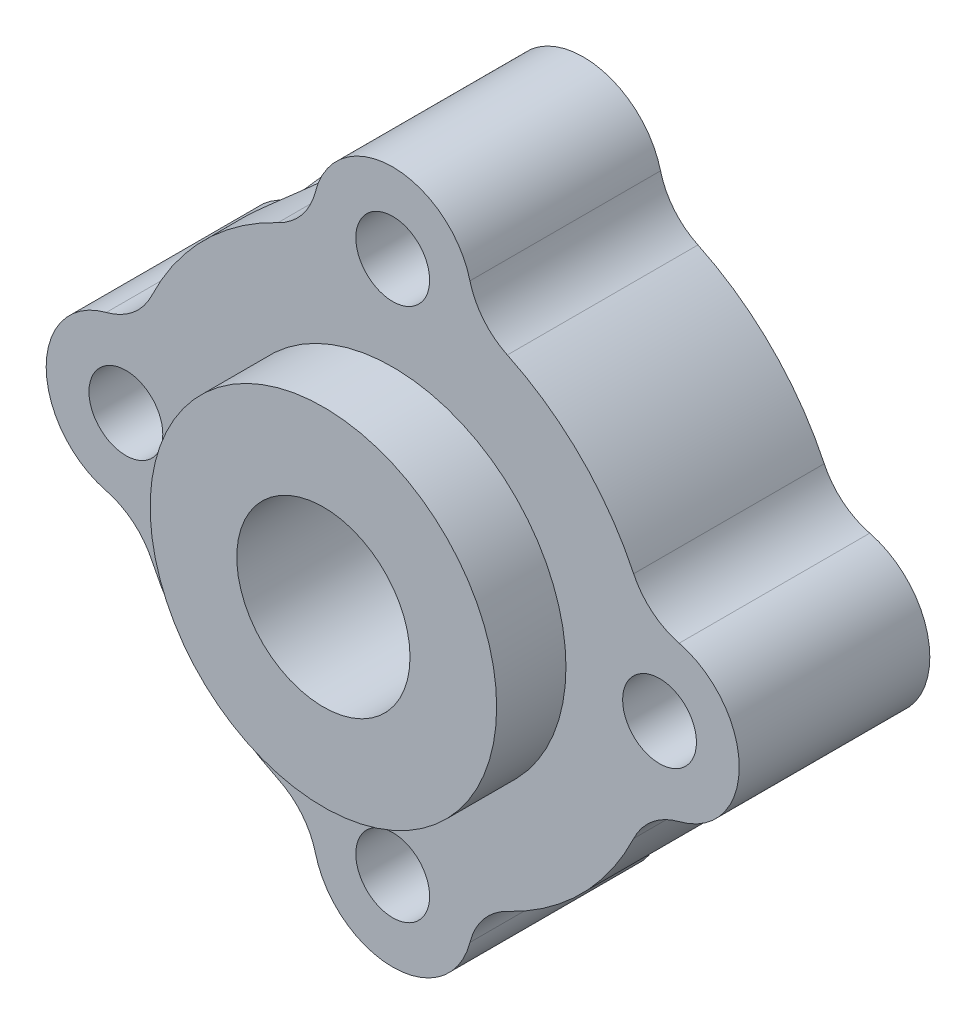
SolidWorks part; units mm, degrees
ref_plane "Front Plane" through (0, 0, 0) normal (0, 0, 1) x (1, 0, 0)
ref_plane "Top Plane" through (0, 0, 0) normal (0, 1, 0) x (1, 0, 0)
ref_plane "Right Plane" through (0, 0, 0) normal (1, 0, 0) x (0, 0, -1)
sketch "Sketch1" plane through (0, 0, 0) normal (0, 0, 1) x (1, 0, 0)
  arc A0 (-21.7959, 25.8991) -> (-28.2504, 19.4446) centre (-18.9077, 16.5564) ccw
  arc A1 (-28.2504, 13.6681) -> (-21.7959, 7.2136) centre (-18.9077, 16.5564) ccw
  arc A2 (-16.0195, 25.8991) -> (-21.7959, 25.8991) centre (-18.9077, 26.3354) ccw
  arc A3 (-21.7959, 7.2136) -> (-16.0195, 7.2136) centre (-18.9077, 6.7774) ccw
  arc A4 (-28.2504, 19.4446) -> (-28.2504, 13.6681) centre (-28.6867, 16.5564) ccw
  arc A5 (-9.565, 13.6681) -> (-9.565, 19.4446) centre (-9.1287, 16.5564) ccw
  arc A6 (-9.565, 19.4446) -> (-16.0195, 25.8991) centre (-18.9077, 16.5564) ccw
  arc A7 (-16.0195, 7.2136) -> (-9.565, 13.6681) centre (-18.9077, 16.5564) ccw
  dimension "D1" = 19.558
extrude "Boss-Extrude2" add sketch "Sketch1" along normal blind 6.985
fillet "Fillet3" radius 2.54 8 edges at (-9.565, 13.6681, 3.4925) (-16.0195, 7.2136, 3.4925) (-21.7959, 7.2136, 3.4925) (-28.2504, 13.6681, 3.4925) (-9.565, 19.4446, 3.4925) (-16.0195, 25.8991, 3.4925) (-21.7959, 25.8991, 3.4925) (-28.2504, 19.4446, 3.4925)
sketch "Sketch2" plane through (0, 0, 6.985) normal (0, 0, 1) x (1, 0, 0)
  line L0 (-31.6077, 16.5564) -> (-6.2077, 16.5564) construction
  arc A0 (-29.4061, 19.3874) -> (-29.4061, 13.7254) centre (-28.6867, 16.5564) ccw construction
  arc A1 (-8.4093, 13.7254) -> (-8.4093, 19.3874) centre (-9.1287, 16.5564) ccw construction
  circle A2 centre (-18.9077, 16.5564) radius 6.35
extrude "Boss-Extrude3" add sketch "Sketch2" along normal blind 2.54
sketch "Sketch3" plane through (0, 0, 9.525) normal (0, 0, 1) x (1, 0, 0)
  line L0 (-25.2577, 16.5564) -> (-12.5577, 16.5564) construction
  circle A0 centre (-18.9077, 16.5564) radius 6.35 construction
  circle A1 centre (-18.9077, 16.5564) radius 3.175
  dimension "D1" = 6.35
extrude "Cut-Extrude1" cut sketch "Sketch3" against normal blind 9.525
sketch "Sketch4" plane through (0, 0, 0) normal (0, 0, -1) x (-1, 0, 0)
  circle A2 centre (18.9077, 16.5564) radius 9.779
  dimension "D1" = 19.558
sketch "Sketch5" plane through (0, 0, 0) normal (0, 0, -1) x (-1, 0, 0)
  line L0 (18.9077, 29.2564) -> (18.9077, 3.8564) construction
  line L1 (6.2077, 16.5564) -> (31.6077, 16.5564) construction
  arc A0 (21.7387, 27.0548) -> (16.0767, 27.0548) centre (18.9077, 26.3354) ccw construction
  arc A1 (16.0767, 6.0579) -> (21.7387, 6.0579) centre (18.9077, 6.7774) ccw construction
  arc A2 (8.4093, 19.3874) -> (8.4093, 13.7254) centre (9.1287, 16.5564) ccw construction
  arc A3 (29.4061, 13.7254) -> (29.4061, 19.3874) centre (28.6867, 16.5564) ccw construction
hole_wizard "#6-32 Tapped Hole1" positions "Sketch7" profile "Sketch6" tap size "#6-32" standard "ANSI Inch" end condition through all
sketch "Sketch7" plane through (0, 0, 0) normal (0, 0, -1) x (-1, 0, 0)
  line L0 (18.9077, 29.2564) -> (18.9077, 3.8564) construction
  line L1 (6.2077, 16.5564) -> (31.6077, 16.5564) construction
  circle A0 centre (18.9077, 16.5564) radius 9.779 construction
  point P0 (18.9077, 26.3354)
  point P6 (28.6867, 16.5564)
  point P9 (18.9077, 6.7774)
  point P12 (9.1287, 16.5564)
sketch "Sketch6" plane through (-18.9077, 26.3354, 0) normal (1, 0, 0) x (0, 1, 0)
  line L0 (0, 0) -> (0, 9.525)
  line L1 (0, 9.525) -> (1.3525, 9.525)
  line L2 (1.3525, 9.525) -> (1.3525, 0)
  line L5 (1.3525, 0) -> (0, 0)
  line L11 (0, -6.35) -> (0, 107.95) construction
  dimension "Thread Major Dia." = 2.7051
  dimension "Thru Tap Drill Depth" = 9.525
extrude "Cut-Extrude4" cut sketch "Sketch12" against normal blind 9.906
sketch "Sketch12" plane through (-24.4343, 24.8373, 0) normal (-0.7013, 0.7129, 0) x (0.7129, 0.7013, 0)
  line L0 (1.2931, 0) -> (-5.2243, -6.9193) construction
  circle A0 centre (-1.9656, -3.4596) radius 2.159
ref_plane "Plane1" through (-24.4343, 24.8373, 0) normal (-0.7013, 0.7129, 0) x (0.7129, 0.7013, 0)
